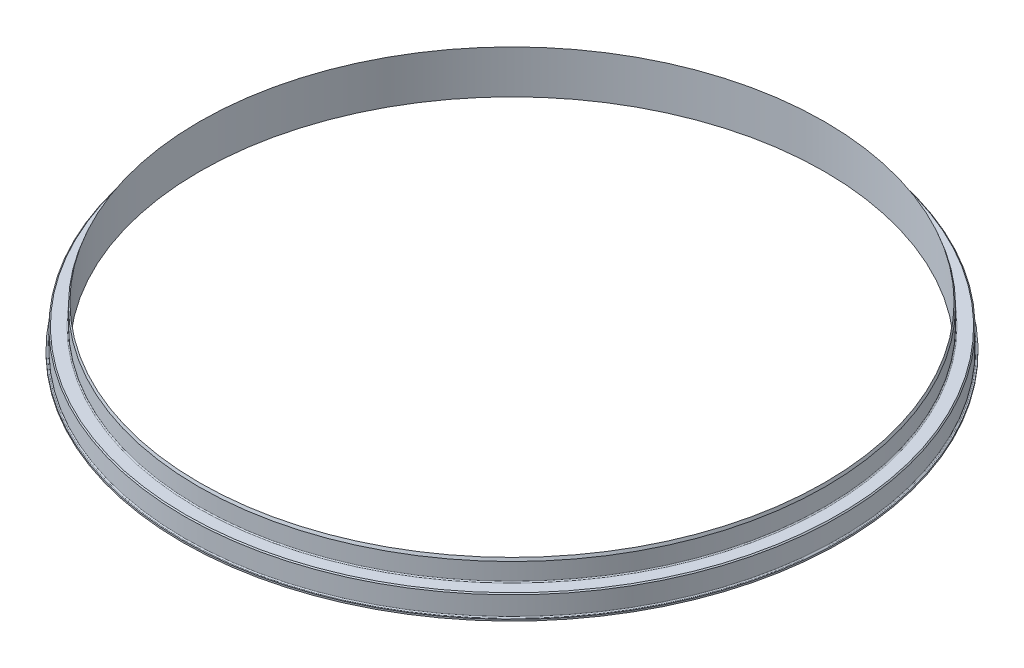
SolidWorks part; units mm, degrees
ref_plane "Front Plane" through (0, 0, 0) normal (0, 0, 1) x (1, 0, 0)
ref_plane "Top Plane" through (0, 0, 0) normal (0, 1, 0) x (1, 0, 0)
ref_plane "Right Plane" through (0, 0, 0) normal (1, 0, 0) x (0, 0, -1)
sketch "Sketch1" plane through (0, 0, 0) normal (0, 0, 1) x (1, 0, 0)
  line L0 (0, 28.739) -> (0, -28.739) construction
  line L1 (0, -11.5951) -> (0, 11.5951) construction
  line L2 (152.4, 28.739) -> (152.4, -28.739) construction
  line L3 (160.655, 28.739) -> (160.655, -28.739) construction
  line L4 (0, 0) -> (160.655, 0) construction
  line L5 (152.4, 21.082) -> (152.4, 0)
  line L6 (152.4, 0) -> (160.655, 0)
  line L7 (159.639, 10.922) -> (159.639, 0.762)
  line L8 (159.639, 10.922) -> (152.908, 10.922)
  line L9 (152.908, 10.922) -> (152.908, 19.6863)
  line L10 (159.639, 0.762) -> (160.655, 0.762)
  line L11 (152.4, 21.082) -> (152.908, 19.6863)
  line L12 (160.655, 0.762) -> (160.655, 0)
  dimension "D1" = 152.4
  dimension "D2" = 160.655
  dimension "D3" = 0.508
  dimension "D5" = 10.16
  dimension "D4" = 6.731
  dimension "D7" = 10.16
  dimension "D8" = 0.762
  dimension "D9" = 1.016
  dimension "D6" = 20
revolve "Revolve1" add sketch "Sketch1" angle 360 about L0
fillet "Fillet1" radius 0.508 2 edges at (0, 10.922, 152.908) (0, 0.762, 159.639)
chamfer "Chamfer1" distance 0.508 angle 45 1 edges at (0, 10.922, 159.639)
equation "\"Di\" = 12.0in"
equation "\"Do\" = 12.65in"
equation "\"Ri\"= \"Di\" / 2"
equation "\"Ro\"= \"Do\" / 2"
equation "\"D1@Sketch1\"=\"Ri\""
equation "\"D2@Sketch1\"=\"Ro\""
